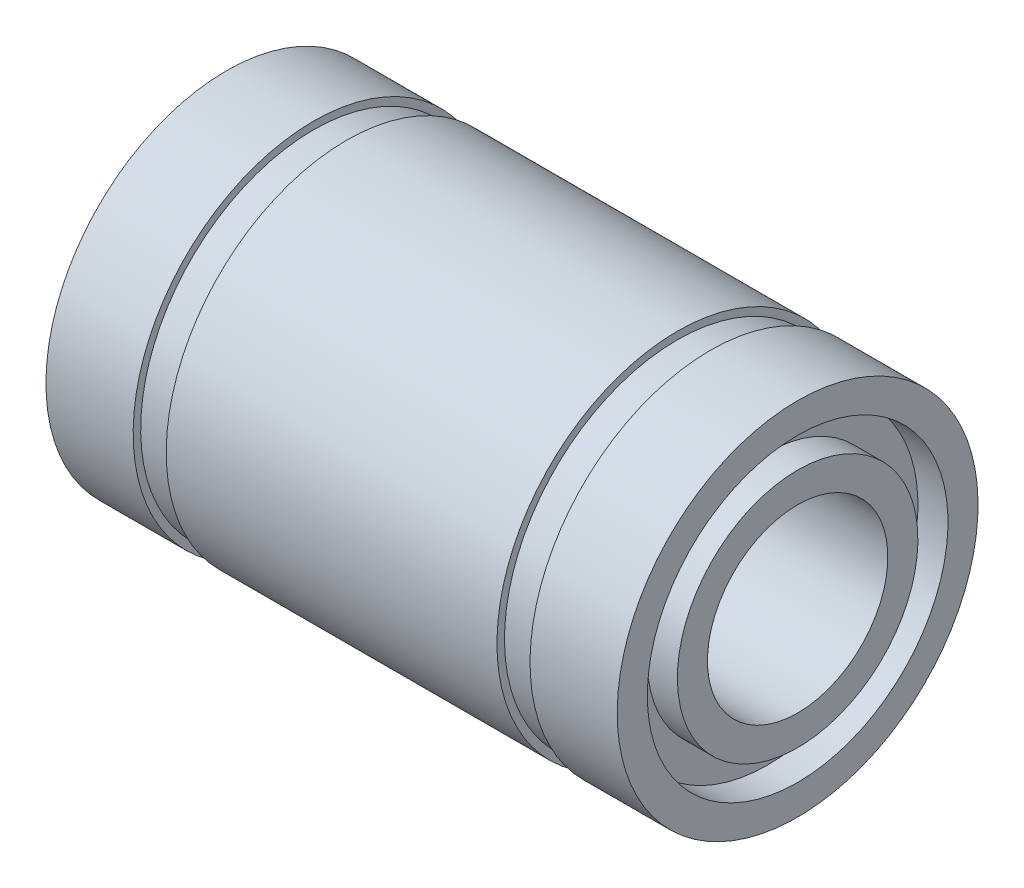
SolidWorks part; units mm, degrees
material "Ст3сп ГОСТ 535-2005"
ref_plane "Plano frontal" through (0, 0, 0) normal (0, 0, 1) x (1, 0, 0)
ref_plane "Plano superior" through (0, 0, 0) normal (0, 1, 0) x (1, 0, 0)
ref_plane "Plano direito" through (0, 0, 0) normal (1, 0, 0) x (0, 0, -1)
sketch "Esboço1" plane through (0, 0, 0) normal (0, 0, 1) x (1, 0, 0)
  line L0 (-9.5, 6) -> (-6.6, 6)
  line L1 (-6.6, 6) -> (-6.6, 5.75)
  line L2 (-6.6, 5.75) -> (-5.5, 5.75)
  line L3 (-5.5, 5.75) -> (-5.5, 6)
  line L4 (-5.5, 6) -> (5.5, 6)
  line L5 (5.5, 6) -> (5.5, 5.75)
  line L6 (5.5, 5.75) -> (6.6, 5.75)
  line L7 (6.6, 5.75) -> (6.6, 6)
  line L8 (6.6, 6) -> (9.5, 6)
  line L9 (9.5, 6) -> (9.5, 5)
  line L10 (9.5, 3) -> (-9.5, 3)
  line L11 (-9.5, 3) -> (-9.5, 4)
  line L12 (0, 3) -> (0, 0) construction
  line L13 (0, 0) -> (-86.5, 0) construction
  line L14 (-9.5, 5) -> (-9.5, 6)
  line L15 (-9.5, 5) -> (-8.5, 5)
  line L16 (9.5, 4) -> (9.5, 3)
  line L17 (-8.5, 5) -> (-8.5, 4)
  line L18 (-8.5, 4) -> (-9.5, 4)
  line L19 (9.5, 5) -> (8.5, 5)
  line L21 (9.5, 4) -> (8.5, 4)
  line L22 (8.5, 5) -> (8.5, 4)
  dimension "D1" = 19
  dimension "D2" = 13.2
  dimension "D3" = 1.1
  dimension "D4" = 6
  dimension "D5" = 12
  dimension "D6" = 11.5
  dimension "D7" = 1
  dimension "D8" = 1
  dimension "D9" = 1
  dimension "D10" = 1
revolve "Revolução1" add sketch "Esboço1" angle 360 about L13
